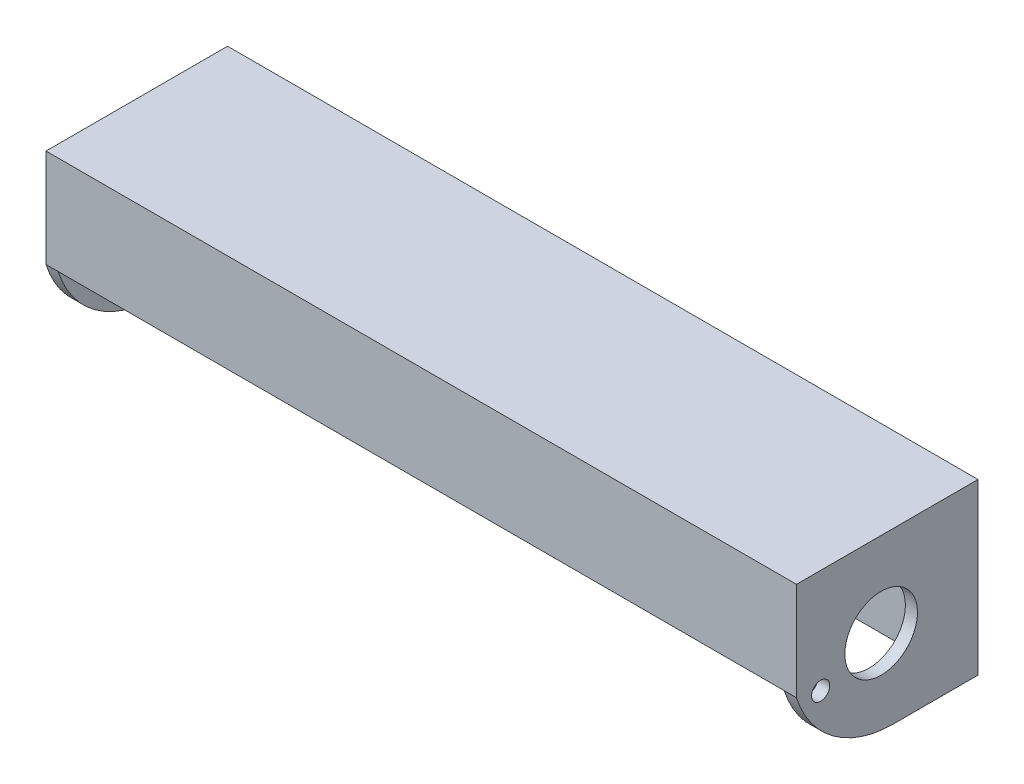
SolidWorks part; units mm, degrees
ref_plane "Front Plane" through (0, 0, 0) normal (0, 0, 1) x (1, 0, 0)
ref_plane "Top Plane" through (0, 0, 0) normal (0, 1, 0) x (1, 0, 0)
ref_plane "Right Plane" through (0, 0, 0) normal (1, 0, 0) x (0, 0, -1)
sketch "Sketch1" plane through (0, 0, 0) normal (0, 0, 1) x (1, 0, 0)
  line L1 (-24.7898, -7.6234) -> (1499.2102, -7.6234)
  line L2 (-24.7898, -7.6234) -> (-24.7898, 347.9766)
  line L3 (-24.7898, 347.9766) -> (1499.2102, 347.9766)
  line L4 (1499.2102, -7.6234) -> (1499.2102, 347.9766)
  dimension "D1" = 1524
  dimension "D2" = 355.6
extrude "Boss-Extrude1" add sketch "Sketch1" along normal blind 25.4
sketch "Sketch5" plane through (-24.7898, 0, 0) normal (-1, 0, 0) x (0, 0, 1)
  line L0 (0, 347.9766) -> (381, 347.9766)
  line L1 (381, 347.9766) -> (381, 141.8618)
  line L2 (0, 347.9766) -> (0, -7.6234)
  line L3 (0, -7.6234) -> (177.8, -7.6234)
  arc A0 (177.8, -7.6234) -> (381, 141.8618) centre (177.8, 205.2273) ccw
  dimension "D1" = 177.8
  dimension "D2" = 381
extrude "Boss-Extrude5" add sketch "Sketch5" along normal blind 25.4
sketch "Sketch6" plane through (-24.7898, 0, 0) normal (1, 0, 0) x (0, 0, -1)
  line L0 (-25.4, 347.9766) -> (-381, 347.9766)
  line L1 (-381, 347.9766) -> (-381, 141.8618)
  line L2 (-381, 141.8618) -> (-381, 347.9766) construction
  line L3 (-381, 141.8618) -> (-368.3, 141.8618)
  line L4 (-368.3, 141.8618) -> (-368.3, 335.2766)
  line L5 (-368.3, 335.2766) -> (-25.4, 335.2766)
  line L6 (-25.4, 347.9766) -> (-25.4, -7.6234) construction
  line L7 (-25.4, 335.2766) -> (-25.4, 347.9766)
  arc A0 (-381, 141.8618) -> (-177.8, -7.6234) centre (-177.8, 205.2273) ccw construction
  dimension "D1" = 12.7
  dimension "D2" = 12.7
extrude "Boss-Extrude6" add sketch "Sketch6" along normal blind 762
ref_plane "Plane2" through (737.2102, 0, 0) normal (1, 0, 0) x (0, 0, -1)
mirror "Mirror2" about plane through (737.2102, 0, 0) normal (1, 0, 0) of "Boss-Extrude5", "Boss-Extrude6"
sketch "Sketch7" plane through (-50.1898, 0, 0) normal (-1, 0, 0) x (0, 0, 1)
  line L0 (0, -7.6234) -> (177.8, -7.6234) construction
  line L1 (0, 347.9766) -> (0, -7.6234) construction
  circle A0 centre (203.2, 170.1766) radius 76.2
  dimension "D1" = 152.4
  dimension "D2" = 177.8
  dimension "D3" = 203.2
extrude "Cut-Extrude1" cut sketch "Sketch7" against normal through all
sketch "Sketch8" plane through (-50.1898, 0, 0) normal (-1, 0, 0) x (0, 0, 1)
  line L0 (381, 141.8618) -> (381, 347.9766) construction
  circle A0 centre (330.2, 129.1618) radius 19.05
  dimension "D1" = 38.1
  dimension "D2" = 50.8
  dimension "D3" = 12.7
extrude "Cut-Extrude2" cut sketch "Sketch8" against normal through all
